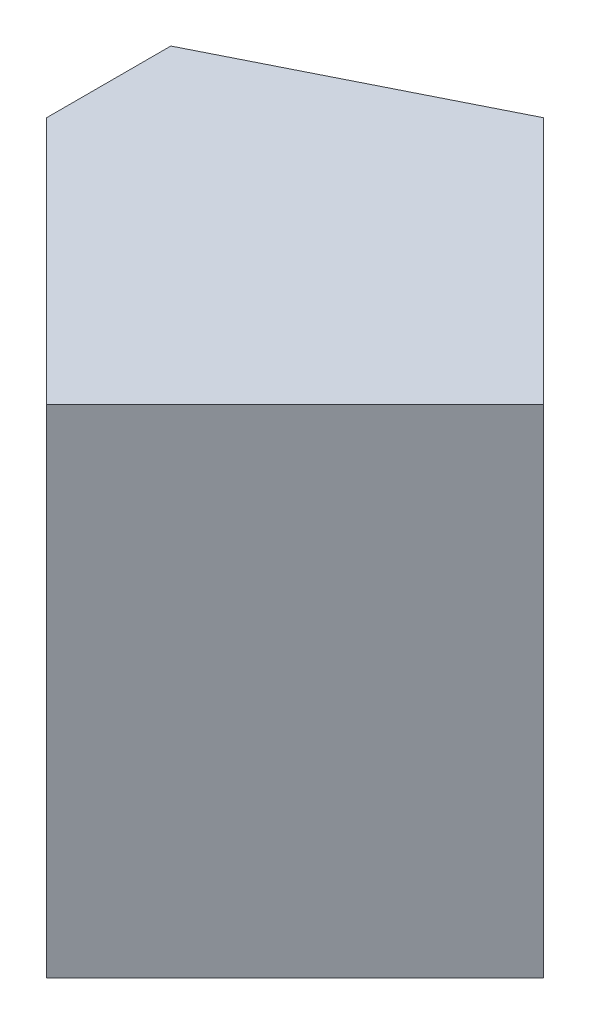
SolidWorks part; units mm, degrees
ref_plane "Front Plane" through (0, 0, 0) normal (0, 0, 1) x (1, 0, 0)
ref_plane "Top Plane" through (0, 0, 0) normal (0, 1, 0) x (1, 0, 0)
ref_plane "Right Plane" through (0, 0, 0) normal (1, 0, 0) x (0, 0, -1)
sketch "Sketch1" plane through (0, 0, 0) normal (0, 0, 1) x (1, 0, 0)
  line L1 (0, 0) -> (20, 0)
  line L2 (0, 0) -> (0, 20)
  line L3 (0, 20) -> (20, 20)
  line L4 (20, 0) -> (20, 20)
  dimension "D1" = 20
  dimension "D2" = 20
extrude "Boss-Extrude1" add sketch "Sketch1" along normal blind 20
sketch "Sketch2" plane through (0, 20, 0) normal (0, 1, 0) x (1, 0, 0)
  line L0 (20, 0) -> (10, 0)
  line L1 (20, 0) -> (0, 0) construction
  line L2 (10, 0) -> (20, -10)
  line L3 (20, -20) -> (20, 0) construction
  line L4 (20, -10) -> (20, 0)
extrude "Cut-Extrude1" cut sketch "Sketch2" against normal blind 20
sketch "Sketch3" plane through (0, 20, 0) normal (0, 1, 0) x (1, 0, 0)
  line L0 (20, -20) -> (10, -20)
  line L1 (20, -20) -> (0, -20) construction
  line L2 (10, -20) -> (20, -10)
  line L3 (20, -10) -> (20, -20)
extrude "Cut-Extrude2" cut sketch "Sketch3" against normal blind 20
sketch "Sketch4" plane through (0, 20, 0) normal (0, 1, 0) x (1, 0, 0)
  line L0 (10, -20) -> (0, -10)
  line L1 (0, -20) -> (0, 0) construction
  line L2 (0, -10) -> (0, -20)
  line L3 (0, -20) -> (10, -20)
extrude "Cut-Extrude3" cut sketch "Sketch4" against normal blind 20
sketch "Sketch5" plane through (0, 20, 0) normal (0, 1, 0) x (1, 0, 0)
  line L0 (10, 0) -> (0, -5)
  line L1 (0, -10) -> (0, 0) construction
  line L2 (0, -5) -> (0, 0)
  line L3 (0, 0) -> (10, 0)
  dimension "D1" = 5
extrude "Cut-Extrude4" cut sketch "Sketch5" against normal blind 20
